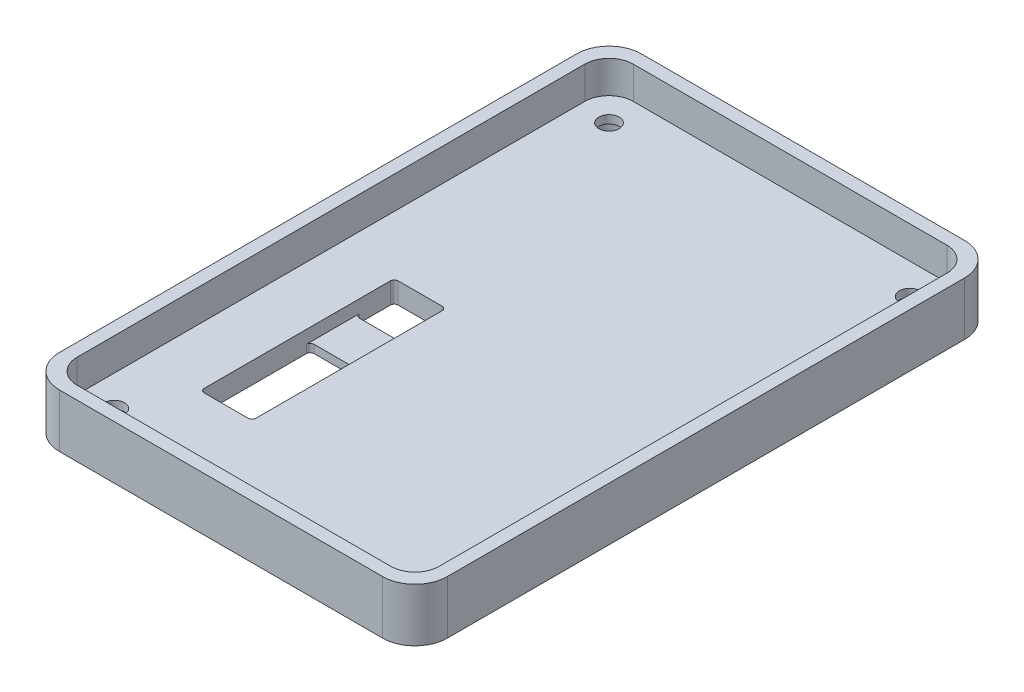
SolidWorks part; units mm, degrees
ref_plane "Front Plane" through (0, 0, 0) normal (0, 0, 1) x (1, 0, 0)
ref_plane "Top Plane" through (0, 0, 0) normal (0, 1, 0) x (1, 0, 0)
ref_plane "Right Plane" through (0, 0, 0) normal (1, 0, 0) x (0, 0, -1)
sketch "Sketch1" plane through (0, 0, 0) normal (0, 1, 0) x (1, 0, 0)
  line L1 (-38.1, -57.15) -> (38.1, -57.15)
  line L2 (-38.1, -57.15) -> (-38.1, 57.15)
  line L3 (-38.1, 57.15) -> (38.1, 57.15)
  line L4 (38.1, -57.15) -> (38.1, 57.15)
  line L5 (-38.1, -57.15) -> (38.1, 57.15) construction
  line L6 (-38.1, 57.15) -> (38.1, -57.15) construction
  point P0 (0, 0)
  dimension "D1" = 76.2
  dimension "D2" = 114.3
extrude "Boss-Extrude1" add sketch "Sketch1" along normal blind 4.1275
sketch "Sketch2" plane through (0, 4.1275, 0) normal (0, 1, 0) x (1, 0, 0)
  line L0 (-35.56, 54.61) -> (35.56, 54.61)
  line L1 (-38.1, 57.15) -> (38.1, 57.15)
  line L2 (-38.1, 57.15) -> (-38.1, -57.15)
  line L3 (-38.1, -57.15) -> (38.1, -57.15)
  line L4 (38.1, 57.15) -> (38.1, -57.15)
  line L5 (35.56, 54.61) -> (35.56, -54.61)
  line L6 (-35.56, -54.61) -> (35.56, -54.61)
  line L7 (-35.56, 54.61) -> (-35.56, -54.61)
  dimension "D1" = 2.54
extrude "Boss-Extrude2" add sketch "Sketch2" along normal blind 6.35
fillet "Fillet1" radius 6.35 4 edges at (-38.1, 5.2388, 57.15) (38.1, 5.2388, 57.15) (38.1, 5.2388, -57.15) (-38.1, 5.2388, -57.15)
fillet "Fillet2" radius 4.7625 4 edges at (35.56, 7.3025, 54.61) (-35.56, 7.3025, 54.61) (35.56, 7.3025, -54.61) (-35.56, 7.3025, -54.61)
sketch "Sketch3" plane through (0, 4.1275, 0) normal (0, 1, 0) x (1, 0, 0)
  line L0 (0, 0) -> (0, 10.3236) construction
  line L1 (0, 0) -> (13.0717, 0) construction
  line L2 (-38.1, 50.8) -> (-38.1, -50.8) construction
  line L3 (31.75, 57.15) -> (-31.75, 57.15) construction
  circle A0 centre (-29.5275, 48.5775) radius 1.9939
  circle A2 centre (29.5275, 48.5775) radius 1.9939
  circle A3 centre (29.5275, -48.5775) radius 1.9939
  circle A4 centre (-29.5275, -48.5775) radius 1.9939
  dimension "D1" = 3.9878
  dimension "D2" = 8.5725
  dimension "D3" = 8.5725
extrude "Cut-Extrude1" cut sketch "Sketch3" against normal through all
sketch "Sketch4" plane through (0, 0, 0) normal (0, -1, 0) x (1, 0, 0)
  line L0 (0, 0) -> (0, 15.3741) construction
  line L1 (0, 0) -> (14.8542, 0) construction
  circle A0 centre (-29.5275, 48.5775) radius 3.5052
  circle A1 centre (29.5275, 48.5775) radius 3.5052
  circle A2 centre (29.5275, -48.5775) radius 3.5052
  circle A3 centre (-29.5275, -48.5775) radius 3.5052
  dimension "D1" = 7.0104
extrude "Cut-Extrude2" cut sketch "Sketch4" against normal blind 2.54
sketch "Sketch5" plane through (0, 0, 0) normal (0, -1, 0) x (1, 0, 0)
  line L0 (-31.75, 57.15) -> (31.75, 57.15) construction
  line L1 (38.1, 50.8) -> (38.1, -50.8) construction
  text T0 "<b>PWR</b>"
  text T1 "<b>USB</b>"
  dimension "D1" = 6.35
  dimension "D2" = 24.13
  dimension "D3" = 6.35
  dimension "D4" = 12.7
extrude "Cut-Extrude3" cut sketch "Sketch5" against normal blind 3.175
sketch "Sketch6" plane through (0, 0, 0) normal (0, -1, 0) x (1, 0, 0)
  line L0 (-31.75, 57.15) -> (31.75, 57.15) construction
  line L1 (-24.13, 37.084) -> (-13.97, 37.084)
  line L2 (-24.13, 37.084) -> (-24.13, 15.494)
  line L3 (-24.13, 15.494) -> (-13.97, 15.494)
  line L4 (-13.97, 37.084) -> (-13.97, 15.494)
  line L5 (-38.1, -50.8) -> (-38.1, 50.8) construction
  line L7 (-24.13, -1.016) -> (-13.97, -1.016)
  line L8 (-24.13, -1.016) -> (-24.13, 6.604)
  line L9 (-24.13, 6.604) -> (-13.97, 6.604)
  line L10 (-13.97, -1.016) -> (-13.97, 6.604)
  dimension "D1" = 20.066
  dimension "D2" = 13.97
  dimension "D3" = 10.16
  dimension "D4" = 21.59
  dimension "D5" = 10.16
  dimension "D6" = 38.1
  dimension "D7" = 7.62
extrude "Cut-Extrude4" cut sketch "Sketch6" against normal through all
sketch "Sketch7" plane through (0, 4.1275, 0) normal (0, 1, 0) x (1, 0, 0)
  line L1 (-24.13, 1.016) -> (-13.97, 1.016)
  line L2 (-24.13, 1.016) -> (-24.13, -37.084)
  line L3 (-24.13, -37.084) -> (-13.97, -37.084)
  line L4 (-13.97, 1.016) -> (-13.97, -37.084)
extrude "Cut-Extrude5" cut sketch "Sketch7" against normal blind 2.54
fillet "Fillet3" radius 0.762 8 edges at (-13.97, 2.0638, 37.084) (-24.13, 2.0638, 37.084) (-24.13, 0.7937, 6.604) (-13.97, 0.7937, 6.604) (-13.97, 2.0638, -1.016) (-24.13, 2.0638, -1.016) (-24.13, 0.7938, 15.494) (-13.97, 0.7937, 15.494)
